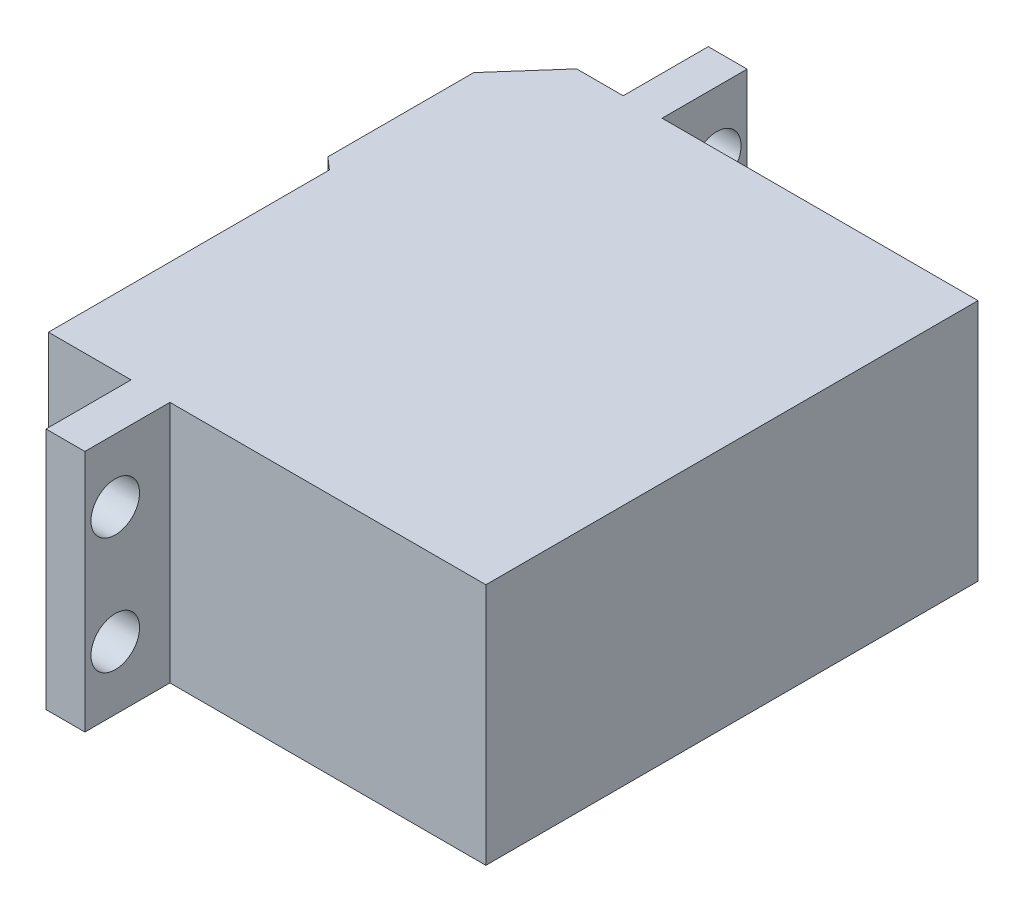
SolidWorks part; units mm, degrees
ref_plane "Front" through (0, 0, 0) normal (0, 0, 1) x (1, 0, 0)
ref_plane "Top" through (0, 0, 0) normal (0, 1, 0) x (1, 0, 0)
ref_plane "Right" through (0, 0, 0) normal (1, 0, 0) x (0, 0, -1)
sketch "Sketch1" plane through (0, 0, 0) normal (0, 1, 0) x (1, 0, 0)
  line L0 (0, 0) -> (0, 40.5)
  line L1 (0, 40.5) -> (-26, 40.5)
  line L2 (-26, 40.5) -> (-26, 47.5)
  line L3 (-26, 47.5) -> (-29.2, 47.5)
  line L4 (-29.2, 47.5) -> (-29.2, 40.5)
  line L5 (-29.2, 40.5) -> (-33.0314, 40.5)
  line L6 (-33.0314, 40.5) -> (-37, 36)
  line L7 (-37, 36) -> (-37, 24)
  line L8 (-37, 24) -> (-36, 23.1181)
  line L9 (-36, 23.1181) -> (-36, 0)
  line L10 (-36, 0) -> (-29.2, 0)
  line L11 (-29.2, 0) -> (-29.2, -7)
  line L12 (-29.2, -7) -> (-26, -7)
  line L13 (-26, -7) -> (-26, 0)
  line L14 (-26, 0) -> (0, 0)
  line L16 (-43, 33) -> (-37, 33) construction
  line L17 (-43, 33) -> (-43, 27) construction
  line L18 (-43, 27) -> (-37, 27) construction
  line L19 (-37, 33) -> (-37, 27) construction
  point P16 (-37, 30)
  point P17 (-43, 30)
  dimension "D1" = 36
  dimension "D2" = 40.5
  dimension "D3" = 7
  dimension "D4" = 26
  dimension "D5" = 3.2
  dimension "D6" = 1
  dimension "D7" = 12
  dimension "D8" = 6
  dimension "D9" = 27
  dimension "D10" = 6
extrude "Boss-Extrude1" add sketch "Sketch1" along normal blind 20
sketch "Sketch2" plane through (-37, 0, 0) normal (-1, 0, 0) x (0, 0, 1)
  line L0 (-30, 0) -> (-30, 20) construction
  line L1 (-33.4641, 10) -> (-31.7321, 7)
  line L2 (-31.7321, 7) -> (-28.2679, 7)
  line L3 (-28.2679, 7) -> (-26.5359, 10)
  line L4 (-26.5359, 10) -> (-28.2679, 13)
  line L5 (-28.2679, 13) -> (-31.7321, 13)
  line L6 (-31.7321, 13) -> (-33.4641, 10)
  line L7 (-36, 0) -> (-24, 0) construction
  line L8 (-36, 20) -> (-24, 20) construction
  line L9 (-36, 10) -> (-24, 10) construction
  line L10 (-36, 20) -> (-36, 0) construction
  line L11 (-24, 20) -> (-24, 0) construction
  circle A0 centre (-30, 10) radius 3 construction
  point P21 (-30, 10)
  dimension "D1" = 6
extrude "Boss-Extrude2" add sketch "Sketch2" along normal blind 4
sketch "Sketch3" plane through (-29.2, 0, 0) normal (-1, 0, 0) x (0, 0, 1)
  line L0 (-47.5, 10) -> (7, 10) construction
  line L1 (-47.5, 20) -> (-47.5, 0) construction
  line L2 (7, 20) -> (7, 0) construction
  line L3 (-20.25, 10) -> (-20.25, 20) construction
  line L4 (-23.1181, 20) -> (0, 20) construction
  line L6 (-40.5, 20) -> (-40.5, 0) construction
  circle A0 centre (-45, 5.2) radius 2
  circle A1 centre (-45, 14.8) radius 2
  circle A2 centre (4.5, 14.8) radius 2
  circle A3 centre (4.5, 5.2) radius 2
  dimension "D1" = 4
  dimension "D2" = 4.5
  dimension "D3" = 9.6
extrude "Cut-Extrude1" cut sketch "Sketch3" against normal through all
sketch "Sketch4" plane through (-41, 0, 0) normal (-1, 0, 0) x (0, 0, 1)
  line L0 (-26.5359, 10) -> (-33.4641, 10) construction
  circle A0 centre (-30, 10) radius 1.5
  point P7 (-30, 10)
  dimension "D1" = 3
extrude "Cut-Extrude2" cut sketch "Sketch4" against normal blind 2
equation "\"`27\"=27.8853"
equation "\"`0.1\"=2"
